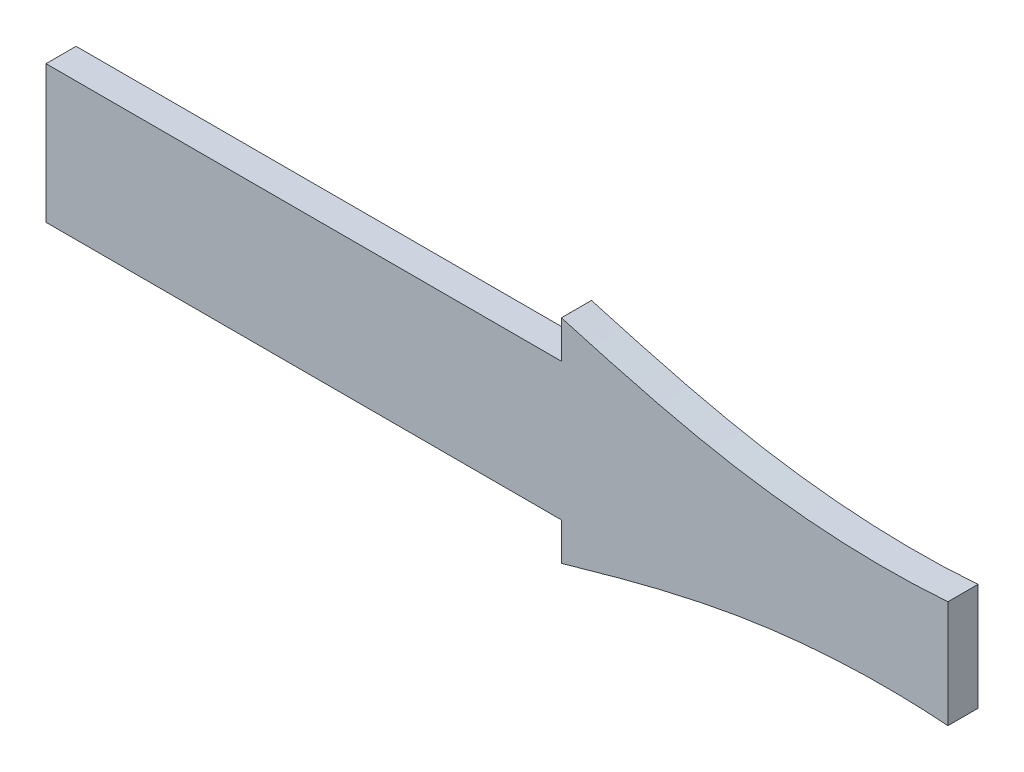
SolidWorks part; units mm, degrees
ref_plane "Front Plane" through (0, 0, 0) normal (0, 0, 1) x (1, 0, 0)
ref_plane "Top Plane" through (0, 0, 0) normal (0, 1, 0) x (1, 0, 0)
ref_plane "Right Plane" through (0, 0, 0) normal (1, 0, 0) x (0, 0, -1)
sketch "Sketch2" plane through (0, 0, 0) normal (0, 0, 1) x (1, 0, 0)
  line L0 (-31.8958, 0) -> (204.9613, 0) construction
  line L1 (204.9613, 0) -> (275.3603, 0) construction
  line L2 (167.9052, 40.0339) -> (167.9052, 25.1287) construction
  line L3 (262.4803, 7.1388) -> (262.4803, -7.1388)
  line L8 (142.548, 9.1372) -> (142.548, -9.1372)
  line L9 (167.9052, -25.1287) -> (167.9052, -32.6173) construction
  line L11 (211.0808, 14.1372) -> (211.0808, 9.1372)
  line L12 (211.0808, 9.1372) -> (142.548, 9.1372)
  line L13 (211.0808, -9.1372) -> (142.548, -9.1372)
  line L14 (211.0808, -14.1372) -> (211.0808, -9.1372)
  spline S0 degree 3 poles (211.0808, 14.1372) (211.9178, 13.8969) (219.4603, 11.7453) (236.2989, 7.3273) (252.9705, 6.4142) (262.4803, 7.1388) knots 0.46088 0.46088 0.46088 0.46088 0.487879 0.704009 1 1 1 1
  spline S1 degree 3 poles (211.0808, -14.1372) (211.9178, -13.8969) (219.4603, -11.7453) (236.2989, -7.3273) (252.9705, -6.4142) (262.4803, -7.1388) knots 0.46088 0.46088 0.46088 0.46088 0.487879 0.704009 1 1 1 1
  point P3 (167.9052, 0)
  point P5 (179.3273, 0)
  point P6 (190.7494, 0)
  point P7 (202.6284, 0)
  point P8 (213.5936, 0)
  point P9 (225.0157, 0)
  point P10 (228.2139, 0)
  point P11 (233.925, 0)
  point P12 (239.6361, 0)
  point P13 (245.3471, 0)
  point P14 (251.0582, 0)
  point P15 (256.7692, 0)
  point P16 (262.4803, 0)
  point P19 (179.3273, 22.2731)
  point P20 (167.9052, 25.1287)
  point P21 (190.7494, 19.9887)
  point P22 (202.6284, 16.7334)
  point P23 (213.5936, 13.421)
  point P24 (225.0157, 10.851)
  point P25 (228.2139, 10.2799)
  point P26 (233.925, 8.5666)
  point P27 (239.6361, 7.4244)
  point P28 (245.3471, 6.8533)
  point P29 (251.0582, 6.8533)
  point P30 (256.7692, 6.8533)
  point P31 (262.4803, 7.1388)
  point P45 (142.548, 0)
  point P46 (211.0808, 14.1372)
  point P47 (211.0808, 0)
  point P48 (211.0808, -14.1372)
  point P55 (142.548, 0)
  dimension "D1" = 5
extrude "Boss-Extrude1" add sketch "Sketch2" along normal blind 4
